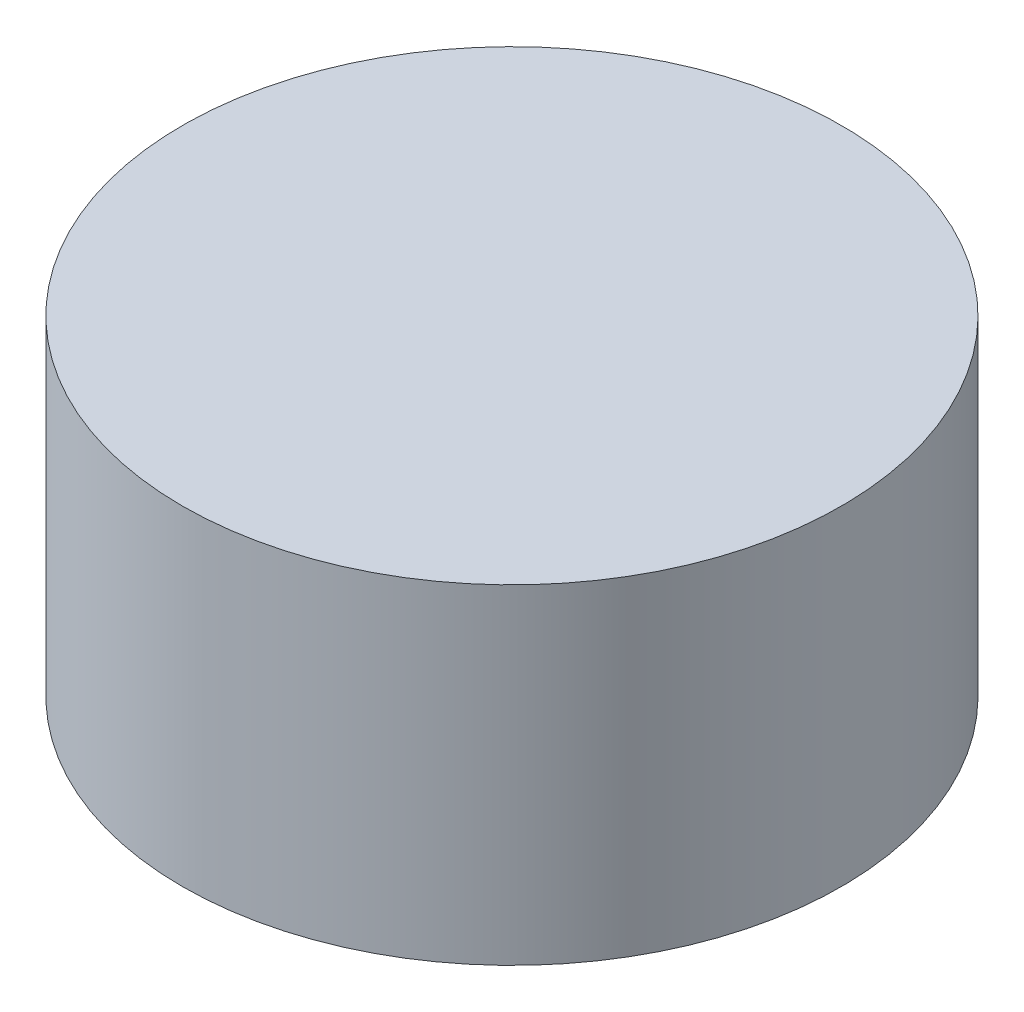
SolidWorks part; units mm, degrees
ref_plane "Front Plane" through (0, 0, 0) normal (0, 0, 1) x (1, 0, 0)
ref_plane "Top Plane" through (0, 0, 0) normal (0, 1, 0) x (1, 0, 0)
ref_plane "Right Plane" through (0, 0, 0) normal (1, 0, 0) x (0, 0, -1)
sketch "Sketch2" plane through (0, 0, 0) normal (0, 1, 0) x (1, 0, 0)
  circle A0 centre (0, 0) radius 50
extrude "Boss-Extrude1" add sketch "Sketch2" along normal blind 50
